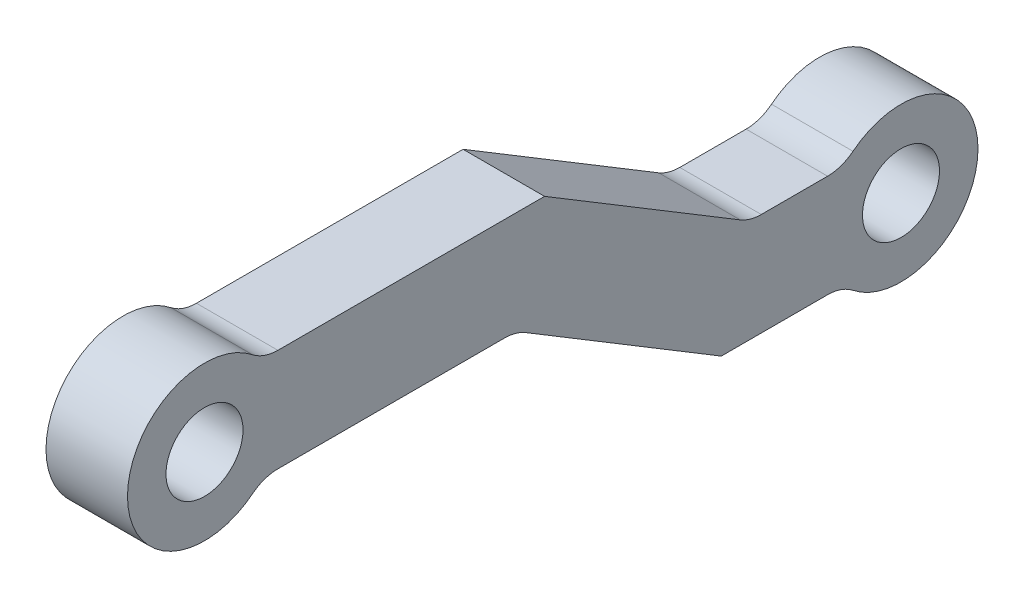
SolidWorks part; units mm, degrees
material "Plain Carbon Steel"
ref_plane "Front Plane" through (0, 0, 0) normal (0, 0, 1) x (1, 0, 0)
ref_plane "Top Plane" through (0, 0, 0) normal (0, 1, 0) x (1, 0, 0)
ref_plane "Right Plane" through (0, 0, 0) normal (1, 0, 0) x (0, 0, -1)
sketch "Sketch2" plane through (0, 0, 0) normal (1, 0, 0) x (0, 0, -1)
  line L16 (2.2361, 2) -> (13.2474, 2)
  line L17 (13.2474, 2) -> (21.2474, -2.8331)
  line L18 (21.2474, -2.8331) -> (24.8968, -2.8331)
  line L19 (0, 0) -> (27.1329, -4.8331) construction
  line L26 (2.2361, -2) -> (12.1329, -2)
  line L27 (12.1329, -2) -> (20.1329, -6.8331)
  line L28 (20.1329, -6.8331) -> (24.8968, -6.8331)
  line L29 (7.7417, 2) -> (7.7417, -2) construction
  line L30 (23.0721, -2.8331) -> (23.0721, -6.8331) construction
  circle A8 centre (0, 0) radius 1.5
  circle A9 centre (27.1329, -4.8331) radius 1.5
  circle A12 centre (0, 0) radius 3
  circle A13 centre (27.1329, -4.8331) radius 3
  point P9 (23.0721, -4.8331)
  point P14 (7.7417, 0)
  dimension "D1" = 10.1
  dimension "D5" = 3
  dimension "D7" = 4
  dimension "D8" = 7
  dimension "D3" = 6
  dimension "D4" = 4
  dimension "D2" = 27.56
  dimension "D6" = 4
  dimension "D9" = 15
extrude "Boss-Extrude1" add sketch "Sketch2" along normal blind 3.175 contours A13 L18 L17 L16 A12 L26 L27 L28 | A8 | A9
fillet "Fillet1" radius 1.5875 6 edges at (1.5875, -6.8331, -24.8968) (1.5875, -2.8331, -21.2474) (1.5875, -2, -12.1329) (1.5875, -2, -2.2361) (1.5875, -2.8331, -24.8968) (1.5875, 2, -2.2361)
